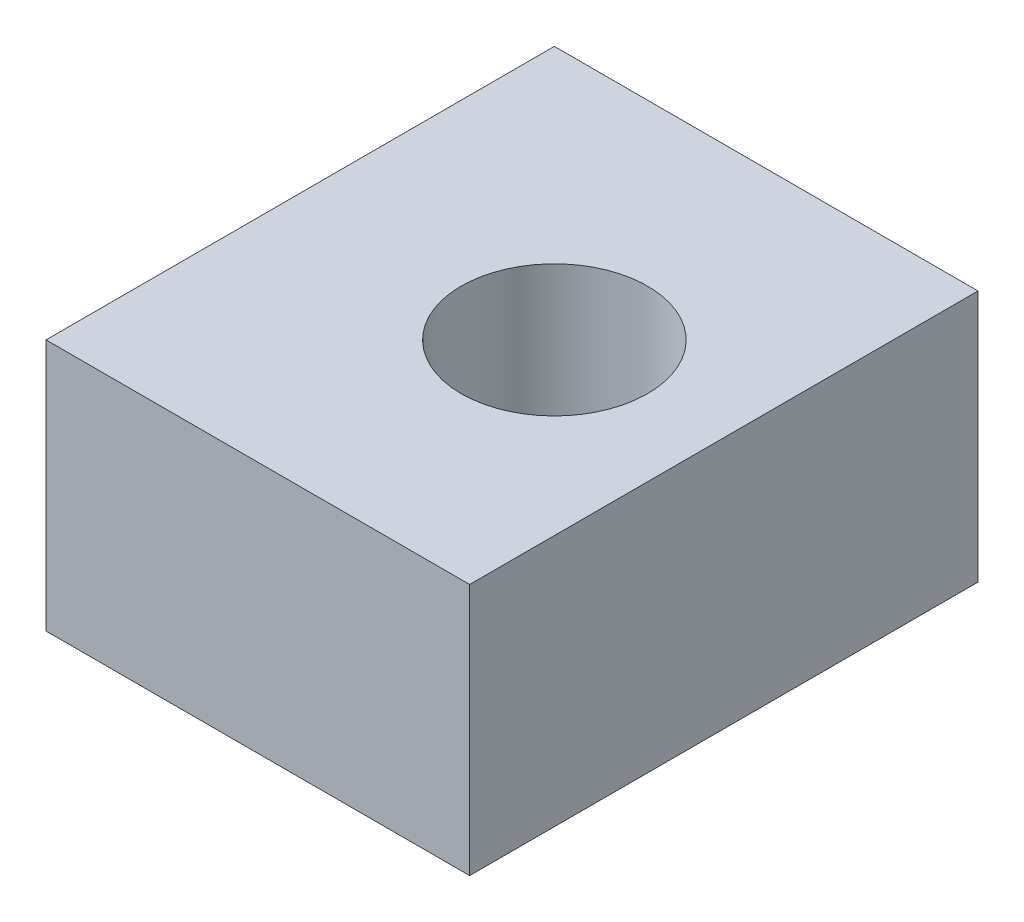
SolidWorks part; units mm, degrees
ref_plane "Front Plane" through (0, 0, 0) normal (0, 0, 1) x (1, 0, 0)
ref_plane "Top Plane" through (0, 0, 0) normal (0, 1, 0) x (1, 0, 0)
ref_plane "Right Plane" through (0, 0, 0) normal (1, 0, 0) x (0, 0, -1)
sketch "Sketch1" plane through (0, 0, 0) normal (0, 1, 0) x (1, 0, 0)
  line L0 (6.35, 0) -> (-9.525, 0) construction
  line L1 (-9.525, 9.525) -> (6.35, 9.525)
  line L2 (-9.525, 9.525) -> (-9.525, -9.525)
  line L3 (-9.525, -9.525) -> (6.35, -9.525)
  line L4 (6.35, 9.525) -> (6.35, -9.525)
  circle A0 centre (0, 0) radius 3.4925
  point P9 (0, 0)
  dimension "D1" = 6.985
  dimension "D2" = 19.05
  dimension "D3" = 6.35
  dimension "D4" = 15.875
extrude "Boss-Extrude1" add sketch "Sketch1" along normal blind 9.4488
